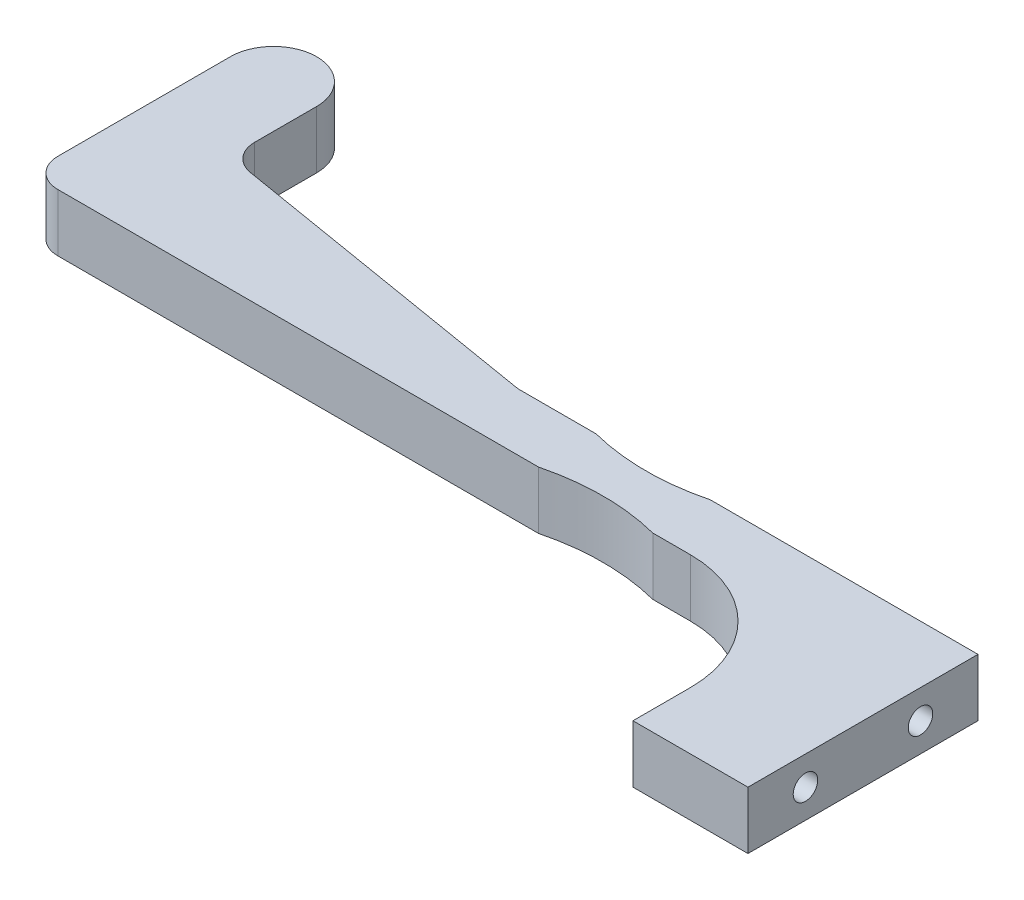
SolidWorks part; units mm, degrees
material "6061-T6 (SS)"
ref_plane "Front Plane" through (0, 0, 0) normal (0, 0, 1) x (1, 0, 0)
ref_plane "Top Plane" through (0, 0, 0) normal (0, 1, 0) x (1, 0, 0)
ref_plane "Right Plane" through (0, 0, 0) normal (1, 0, 0) x (0, 0, -1)
sketch "Sketch1" plane through (0, 0, 0) normal (0, 1, 0) x (1, 0, 0)
  line L0 (4.7625, -4.7625) -> (4.7625, -14.2875)
  line L1 (93.6625, -20.6375) -> (80.9625, -20.6375)
  line L2 (93.6625, -20.6375) -> (93.6625, -46.0375)
  line L3 (-4.7625, -4.7625) -> (-4.7625, -26.9875)
  line L4 (-4.7625, -26.9875) -> (80.9625, -26.9875)
  line L5 (80.9625, -26.9875) -> (80.9625, -46.0375)
  line L6 (80.9625, -46.0375) -> (93.6625, -46.0375)
  line L7 (80.9625, -20.6375) -> (42.8625, -20.6375)
  line L8 (42.8625, -20.6375) -> (4.7625, -14.2875)
  arc A0 (4.7625, -4.7625) -> (-4.7625, -4.7625) centre (0, -4.7625) ccw
  dimension "D1" = 6.35
  dimension "D2" = 9.525
  dimension "D3" = 38.1
  dimension "D4" = 12.7
  dimension "D5" = 12.7
  dimension "D6" = 19.05
  dimension "D7" = 9.525
  dimension "D8" = 38.1
extrude "Boss-Extrude1" add sketch "Sketch1" along normal blind 6.35
fillet "Fillet1" radius 3.175 3 edges at (42.8625, 3.175, 20.6375) (4.7625, 3.175, 14.2875) (-4.7625, 3.175, 26.9875)
fillet "Fillet2" radius 12.7 1 edges at (80.9625, 3.175, 26.9875)
hole_wizard "#6-32 Tapped Hole1" positions "Sketch2" profile "Sketch3" tap size "#6-32" standard "ANSI Inch"
sketch "Sketch2" plane through (93.6625, 0, 0) normal (1, 0, 0) x (0, 0, -1)
  line L0 (-46.0375, 0) -> (-20.6375, 0) construction
  line L1 (-46.0375, 6.35) -> (-46.0375, 0) construction
  point P0 (-39.6875, 3.175)
  point P2 (-26.9875, 3.175)
  dimension "D1" = 12.7
  dimension "D2" = 3.175
  dimension "D3" = 6.35
cosmetic thread "Hole Thread1"
cosmetic thread "Hole Thread2"
sketch "Sketch3" plane through (93.6625, 3.175, 39.6875) normal (0, 1, 0) x (0, 0, -1)
  line L0 (0, 0) -> (0, 17.4751)
  line L1 (0, 17.4751) -> (1.3525, 16.6624)
  line L2 (1.3525, 16.6624) -> (1.3525, 0)
  line L5 (1.3525, 0) -> (0, 0)
  line L10 (0, 17.4751) -> (-1.3525, 16.6624) construction
  line L11 (0, -6.35) -> (0, 107.95) construction
  dimension "Tap Drill Dia." = 2.7051
  dimension "Tap Drill Depth" = 16.6624
  dimension "Drill Angle" = 118
sketch "Sketch4" plane through (0, 6.35, 0) normal (0, 1, 0) x (1, 0, 0)
  line L0 (57.8048, 3.9688) -> (57.8048, -20.6375) construction
  line L1 (93.6625, -20.6375) -> (43.1253, -20.6375) construction
  line L4 (57.8048, -51.5937) -> (57.8048, -26.9875) construction
  line L5 (-1.5875, -26.9875) -> (68.2625, -26.9875) construction
  line L6 (40.7799, -32.744) -> (74.8297, -32.744)
  line L7 (40.6104, -14.7265) -> (74.9993, -14.7265)
  arc A0 (40.6104, -14.7265) -> (74.9993, -14.7265) centre (57.8048, 3.9688) ccw
  arc A1 (74.8297, -32.744) -> (40.7799, -32.744) centre (57.8048, -51.5937) ccw
  point P1 (74.8297, -14.7265)
  dimension "D1" = 4.7625
  dimension "D2" = 50.8
extrude "Cut-Extrude1" cut sketch "Sketch4" against normal through all
